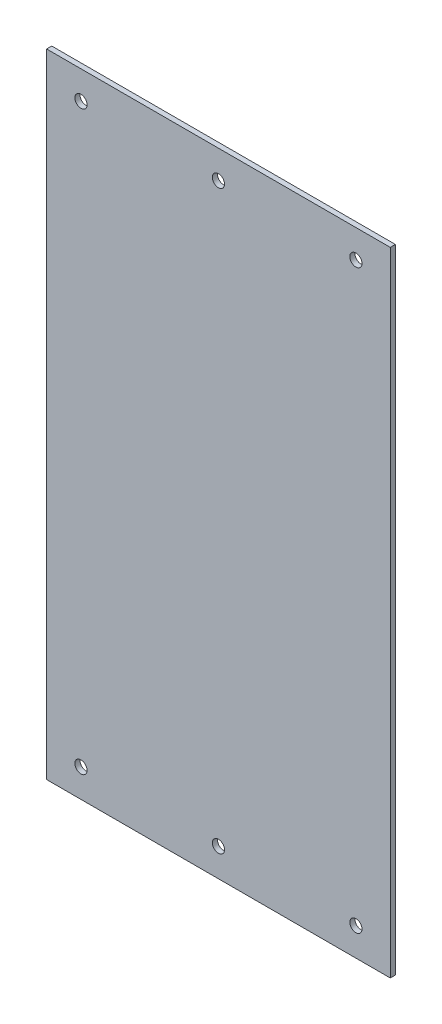
SolidWorks part; units mm, degrees
material "5052-H32"
ref_plane "Front Plane" through (0, 0, 0) normal (0, 0, 1) x (1, 0, 0)
ref_plane "Top Plane" through (0, 0, 0) normal (0, 1, 0) x (1, 0, 0)
ref_plane "Right Plane" through (0, 0, 0) normal (1, 0, 0) x (0, 0, -1)
sketch "Sketch1" plane through (0, 0, 0) normal (0, 0, 1) x (1, 0, 0)
  line L0 (55, 0) -> (-55, 0) construction
  line L1 (-77.5, 142.695) -> (77.5, 142.695)
  line L2 (-77.5, 142.695) -> (-77.5, -142.695)
  line L3 (-77.5, -142.695) -> (77.5, -142.695)
  line L4 (77.5, 142.695) -> (77.5, -142.695)
  line L5 (-77.5, 142.695) -> (77.5, -142.695) construction
  line L6 (-77.5, -142.695) -> (77.5, 142.695) construction
  point P0 (0, 0)
  point P5 (-62, 129.995)
  point P7 (0, 129.995)
  point P8 (62, 129.995)
  point P13 (62, -129.995)
  point P14 (0, -129.995)
  point P15 (-62, -129.995)
  dimension "D1" = 155
  dimension "D2" = 285.39
  dimension "D3" = 15.5
  dimension "D4" = 15.5
  dimension "D5" = 12.7
extrude "Boss-Extrude1" add sketch "Sketch1" along normal blind 2.305
hole_wizard "M5 Clearance Hole1" positions "Sketch2" profile "Sketch3" hole size "M5" standard "ANSI Metric" end condition through all
sketch "Sketch2" plane through (0, 0, 2.305) normal (0, 0, 1) x (1, 0, 0)
  point P0 (-62, 129.995)
  point P3 (0, 129.995)
  point P6 (62, 129.995)
  point P9 (-62, -129.995)
  point P12 (0, -129.995)
  point P15 (62, -129.995)
sketch "Sketch3" plane through (-62, 129.995, 2.305) normal (1, 0, 0) x (0, -1, 0)
  line L0 (0, 0) -> (0, 2.305)
  line L1 (0, 2.305) -> (2.75, 2.305)
  line L2 (2.75, 2.305) -> (2.75, 0)
  line L5 (2.75, 0) -> (0, 0)
  line L11 (0, -6.35) -> (0, 107.95) construction
  dimension "Thru Hole Dia." = 5.5
  dimension "Thru Hole Depth" = 2.305
